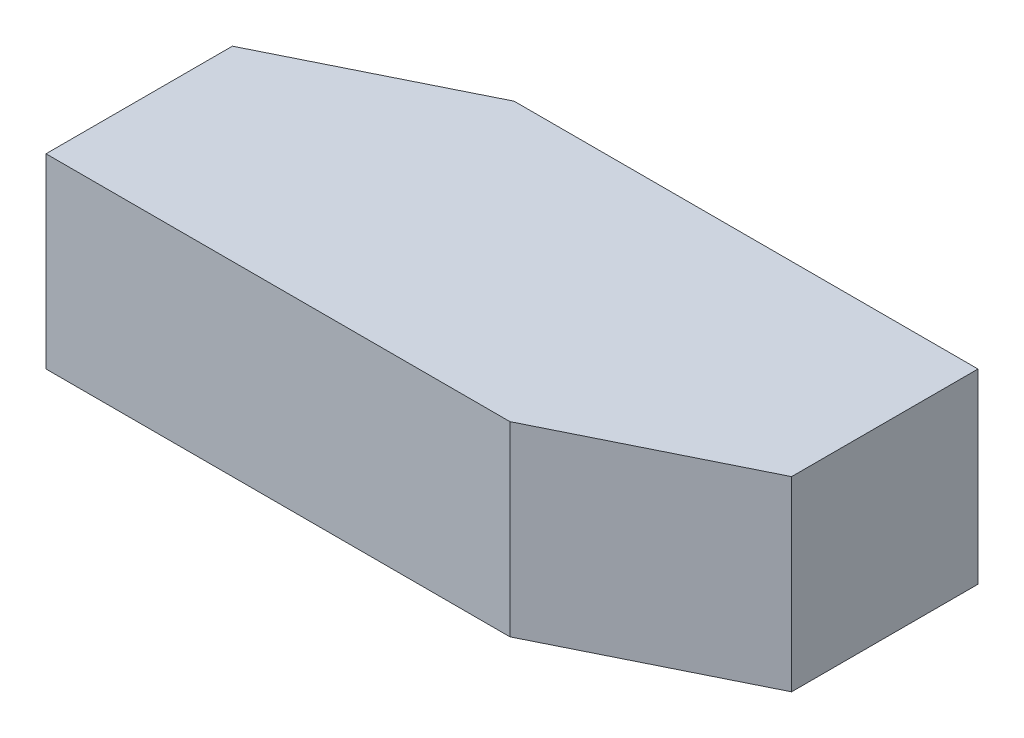
SolidWorks part; units mm, degrees
material "Silicon"
ref_plane "Front Plane" through (0, 0, 0) normal (0, 0, 1) x (1, 0, 0)
ref_plane "Top Plane" through (0, 0, 0) normal (0, 1, 0) x (1, 0, 0)
ref_plane "Right Plane" through (0, 0, 0) normal (1, 0, 0) x (0, 0, -1)
sketch "Sketch1" plane through (0, 0, 0) normal (0, 1, 0) x (1, 0, 0)
  line L12 (-14.6712, -23.6516) -> (-4.7158, -23.6516)
  line L13 (-4.7158, -23.6516) -> (-0.6712, -21.6516)
  line L14 (-0.6712, -21.6516) -> (-0.6712, -17.6516)
  line L15 (-0.6712, -17.6516) -> (-10.6266, -17.6516)
  line L16 (-10.6266, -17.6516) -> (-14.6712, -19.6516)
  line L17 (-14.6712, -19.6516) -> (-14.6712, -23.6516)
  dimension "D1" = 14
  dimension "D2" = 6
  dimension "D7" = 4
extrude "Boss-Extrude1" add sketch "Sketch1" along normal blind 4
